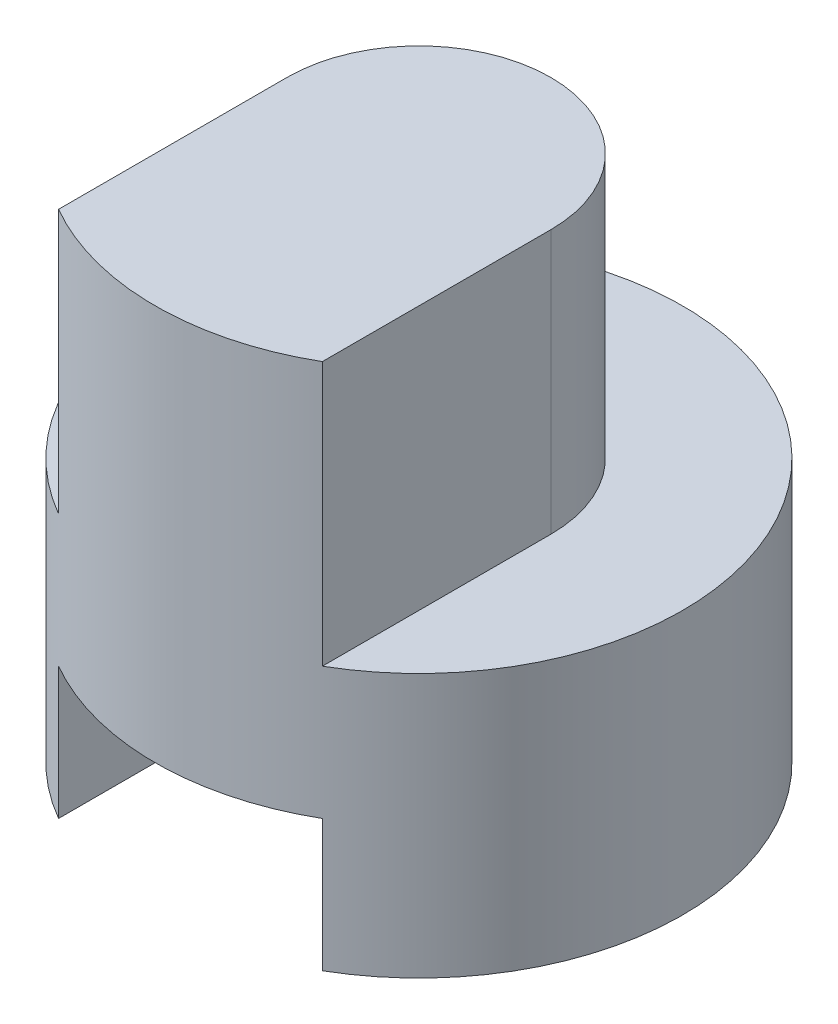
SolidWorks part; units mm, degrees
ref_plane "Front" through (0, 0, 0) normal (0, 0, 1) x (1, 0, 0)
ref_plane "Top" through (0, 0, 0) normal (0, 1, 0) x (1, 0, 0)
ref_plane "Right" through (0, 0, 0) normal (1, 0, 0) x (0, 0, -1)
sketch "Sketch1" plane through (0, 0, 0) normal (0, 1, 0) x (1, 0, 0)
  circle A0 centre (0, 0) radius 2
  dimension "D1" = 4
extrude "Boss-Extrude1" add sketch "Sketch1" along normal blind 2
sketch "Sketch2" plane through (0, 2, 0) normal (0, 1, 0) x (1, 0, 0)
  line L0 (-1, -1.7321) -> (-1, 0)
  line L1 (1, 0) -> (1, -1.7321)
  circle A0 centre (0, 0) radius 2 construction
  arc A1 (-1, 0) -> (1, 0) centre (0, 0) cw
  arc A2 (-1, -1.7321) -> (1, -1.7321) centre (0, 0) ccw
  dimension "D1" = 2
extrude "Boss-Extrude2" add sketch "Sketch2" along normal blind 2
sketch "Sketch3" plane through (0, 0, 0) normal (0, -1, 0) x (1, 0, 0)
  line L0 (-1, 1.7321) -> (-1, 0)
  line L1 (1, 0) -> (1, 1.7321)
  arc A0 (-1, 0) -> (1, 0) centre (0, 0) ccw
  arc A1 (-1, 0) -> (1, 0) centre (0, 0) ccw construction
  arc A2 (-1, 1.7321) -> (1, 1.7321) centre (0, 0) cw
extrude "Cut-Extrude1" cut sketch "Sketch3" against normal blind 1
